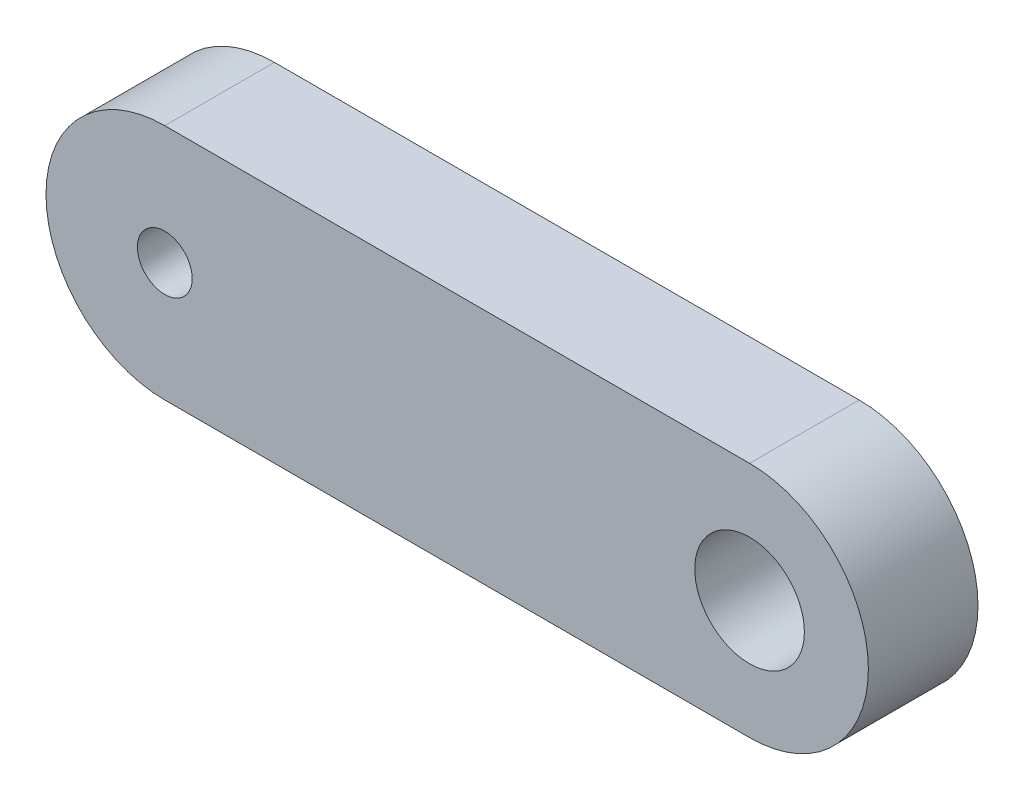
SolidWorks part; units mm, degrees
ref_plane "Front Plane" through (0, 0, 0) normal (0, 0, 1) x (1, 0, 0)
ref_plane "Top Plane" through (0, 0, 0) normal (0, 1, 0) x (1, 0, 0)
ref_plane "Right Plane" through (0, 0, 0) normal (1, 0, 0) x (0, 0, -1)
sketch "Sketch1" plane through (0, 0, 0) normal (0, 0, 1) x (1, 0, 0)
  line L0 (-8, 0) -> (8, 0) construction
  line L1 (-8, 3.25) -> (8, 3.25)
  line L2 (-8, -3.25) -> (8, -3.25)
  arc A0 (-8, 3.25) -> (-8, -3.25) centre (-8, 0) ccw
  arc A1 (8, -3.25) -> (8, 3.25) centre (8, 0) ccw
  circle A2 centre (-8, 0) radius 0.75
  circle A3 centre (8, 0) radius 1.5
  point P2 (0, 0)
  dimension "D3" = 1.5
  dimension "D4" = 3
  dimension "D1" = 16
  dimension "D2" = 6.5
extrude "Boss-Extrude1" add sketch "Sketch1" along normal mid plane 3
